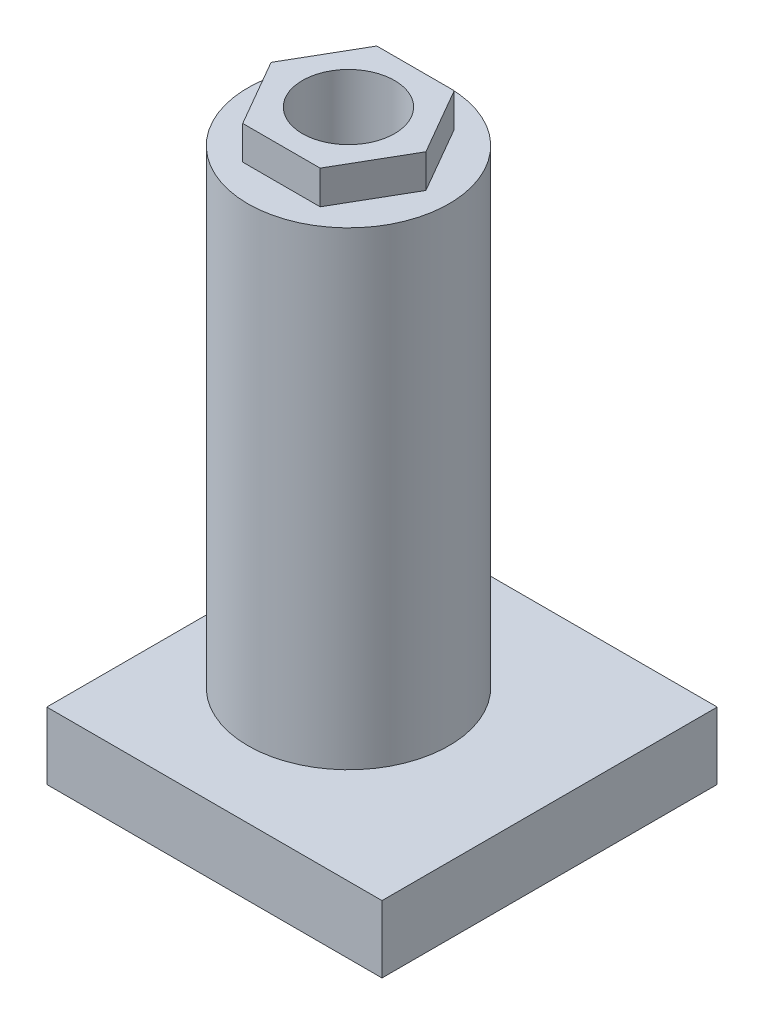
SolidWorks part; units mm, degrees
ref_plane "Front Plane" through (0, 0, 0) normal (0, 0, 1) x (1, 0, 0)
ref_plane "Top Plane" through (0, 0, 0) normal (0, 1, 0) x (1, 0, 0)
ref_plane "Right Plane" through (0, 0, 0) normal (1, 0, 0) x (0, 0, -1)
sketch "Sketch1" plane through (0, 0, 0) normal (0, 1, 0) x (1, 0, 0)
  line L1 (-63.5, 63.5) -> (63.5, 63.5)
  line L2 (-63.5, 63.5) -> (-63.5, -63.5)
  line L3 (-63.5, -63.5) -> (63.5, -63.5)
  line L4 (63.5, 63.5) -> (63.5, -63.5)
  line L5 (-63.5, 63.5) -> (63.5, -63.5) construction
  line L6 (-63.5, -63.5) -> (63.5, 63.5) construction
  point P0 (0, 0)
  dimension "D1" = 127
  dimension "D2" = 127
extrude "Boss-Extrude1" add sketch "Sketch1" along normal blind 25.4
sketch "Sketch2" plane through (0, 25.4, 0) normal (0, 1, 0) x (1, 0, 0)
  line L0 (-12.7, 0) -> (0, 0) construction
  line L1 (-63.5, 63.5) -> (-63.5, -63.5) construction
  circle A0 centre (-12.7, 0) radius 38.1
  dimension "D1" = 76.2
  dimension "D2" = 50.8
extrude "Boss-Extrude2" add sketch "Sketch2" along normal blind 177.8
sketch "Sketch3" plane through (0, 203.2, 0) normal (0, 1, 0) x (1, 0, 0)
  line L1 (16.6294, 0) -> (1.9647, 25.4)
  line L2 (1.9647, 25.4) -> (-27.3647, 25.4)
  line L3 (-27.3647, 25.4) -> (-42.0294, 0)
  line L4 (-42.0294, 0) -> (-27.3647, -25.4)
  line L5 (-27.3647, -25.4) -> (1.9647, -25.4)
  line L6 (1.9647, -25.4) -> (16.6294, 0)
  circle A0 centre (-12.7, 0) radius 25.4 construction
  dimension "D1" = 50.8
extrude "Boss-Extrude3" add sketch "Sketch3" along normal blind 12.7
sketch "Sketch4" plane through (0, 215.9, 0) normal (0, 1, 0) x (1, 0, 0)
  circle A0 centre (-12.7, 0) radius 17.4625
  dimension "D1" = 34.925
extrude "Cut-Extrude1" cut sketch "Sketch4" against normal blind 152.4
sketch "Sketch5" plane through (0, 0, 0) normal (0, -1, 0) x (1, 0, 0)
  line L0 (-63.5, 0) -> (63.5, 0) construction
  line L1 (-63.5, -63.5) -> (-63.5, 63.5) construction
  line L2 (63.5, 63.5) -> (63.5, -63.5) construction
  line L3 (0, 63.5) -> (0, -63.5) construction
  line L4 (-63.5, 63.5) -> (63.5, 63.5) construction
  line L5 (63.5, -63.5) -> (-63.5, -63.5) construction
